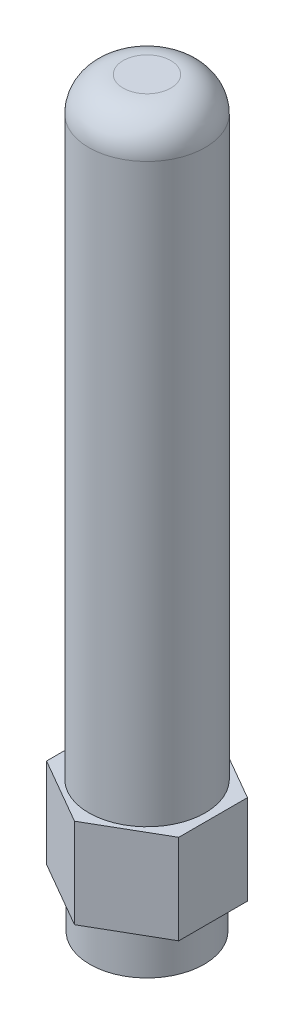
SolidWorks part; units mm, degrees
ref_plane "Front Plane" through (0, 0, 0) normal (0, 0, 1) x (1, 0, 0)
ref_plane "Top Plane" through (0, 0, 0) normal (0, 1, 0) x (1, 0, 0)
ref_plane "Right Plane" through (0, 0, 0) normal (1, 0, 0) x (0, 0, -1)
sketch "Sketch1" plane through (0, 0, 0) normal (0, 1, 0) x (1, 0, 0)
  circle A0 centre (0, 0) radius 3.81
  circle A1 centre (0, 0) radius 2.667
  dimension "D1" = 7.62
  dimension "D2" = 1.143
extrude "Boss-Extrude1" add sketch "Sketch1" along normal blind 2.794
sketch "Sketch3" plane through (0, 2.794, 0) normal (0, 1, 0) x (1, 0, 0)
  line L0 (0, 0) -> (-5.8421, 0) construction
  line L1 (0, 0) -> (0, 7.2085) construction
  line L2 (-4.3994, -2.286) -> (-4.3994, 2.286)
  line L3 (-4.3994, 2.286) -> (0, 4.826)
  line L4 (4.3994, -2.286) -> (4.3994, 2.286)
  line L5 (4.3994, 2.286) -> (0, 4.826)
  line L6 (4.3994, -2.286) -> (0, -4.826)
  line L7 (-4.3994, -2.286) -> (0, -4.826)
  point P14 (4.3994, 0)
  point P15 (-4.3994, 0)
  dimension "D1" = 5.08
  dimension "D2" = 2.286
  dimension "D3" = 120
extrude "Boss-Extrude2" add sketch "Sketch3" along normal blind 5.969
sketch "Sketch4" plane through (0, 8.763, 0) normal (0, 1, 0) x (1, 0, 0)
  circle A0 centre (0, 0) radius 3.8735
  dimension "D1" = 7.747
extrude "Boss-Extrude3" add sketch "Sketch4" along normal blind 40.64
fillet "Fillet1" radius 2.286 1 edges at (0, 49.403, 3.8735)
